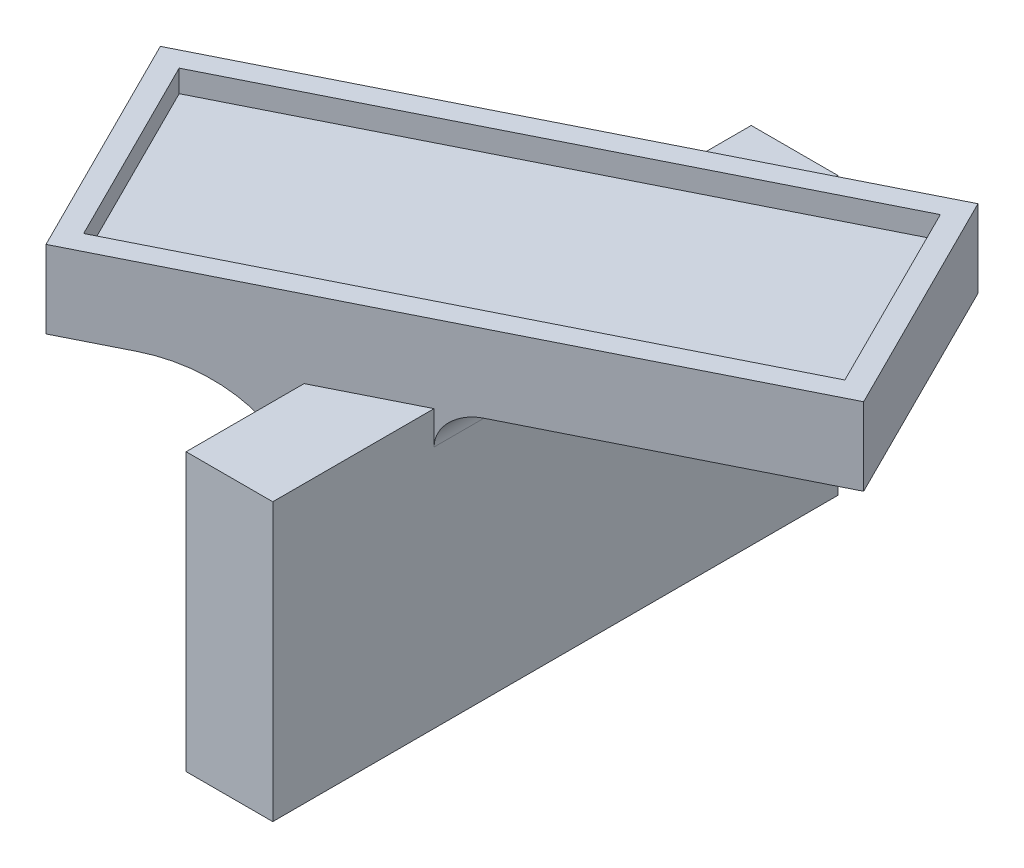
SolidWorks part; units mm, degrees
material "ABS"
ref_plane "Front Plane" through (0, 0, 0) normal (0, 0, 1) x (1, 0, 0)
ref_plane "Top Plane" through (0, 0, 0) normal (0, 1, 0) x (1, 0, 0)
ref_plane "Right Plane" through (0, 0, 0) normal (1, 0, 0) x (0, 0, -1)
sketch "Sketch1" plane through (0, 0, 0) normal (0, 1, 0) x (1, 0, 0)
  line L1 (-3.91, -25.5) -> (3.91, -25.5)
  line L2 (-3.91, -25.5) -> (-3.91, 25.5)
  line L3 (-3.91, 25.5) -> (3.91, 25.5)
  line L4 (3.91, -25.5) -> (3.91, 25.5)
  line L5 (-3.91, -25.5) -> (3.91, 25.5) construction
  line L6 (-3.91, 25.5) -> (3.91, -25.5) construction
  point P0 (0, 0)
extrude "Boss-Extrude1" add sketch "Sketch1" along normal blind 25
sketch "Sketch2" plane through (0, 25, 0) normal (0, 1, 0) x (1, 0, 0)
  line L0 (0, 0) -> (64.6527, 0) construction
  line L1 (4.3382, -8.6764) -> (-21.5791, 43.1582) construction
  line L2 (32.4868, 26.9038) -> (18.5437, 19.9323)
  line L3 (18.5437, 19.9323) -> (27.0721, 2.8756)
  line L4 (27.0721, 2.8756) -> (-18.5437, -19.9323)
  line L5 (-18.5437, -19.9323) -> (-27.0721, -2.8756)
  line L6 (-27.0721, -2.8756) -> (32.4868, 26.9038)
  line L7 (-27.0721, -2.8756) -> (27.0721, 2.8756) construction
  line L8 (18.5437, 19.9323) -> (-18.5437, -19.9323) construction
  line L9 (-19.4381, -22.6156) -> (29.7554, 1.9812)
  line L10 (-3.91, -25.5) -> (3.91, -25.5) construction
  line L11 (29.7554, 1.9812) -> (19.4381, 22.6156)
  line L12 (19.4381, 22.6156) -> (-29.7554, -1.9812)
  line L13 (-29.7554, -1.9812) -> (-19.4381, -22.6156)
  point P5 (0, 0)
  point P12 (0, 0)
  dimension "D1" = 25.5
  dimension "D2" = 51
  dimension "D3" = 25.5
  dimension "D4" = 90
  dimension "D5" = 0
  dimension "D6" = 63.435
  dimension "D7" = 19.07
  dimension "D8" = 2
  dimension "D9" = 2
  dimension "D10" = 2
  dimension "D11" = 2
extrude "Boss-Extrude2" add sketch "Sketch2" along normal blind 5 contours L12 L13 L9 L11
sketch "Sketch3" plane through (0, 30, 0) normal (0, 1, 0) x (1, 0, 0)
  line L0 (-29.7554, -1.9812) -> (-19.4381, -22.6156) construction
  line L1 (19.4381, 22.6156) -> (-29.7554, -1.9812) construction
  line L2 (29.7554, 1.9812) -> (19.4381, 22.6156) construction
  line L4 (29.7554, 1.9812) -> (19.4381, 22.6156)
  line L5 (19.4381, 22.6156) -> (-29.7554, -1.9812)
  line L6 (-29.7554, -1.9812) -> (-19.4381, -22.6156)
  line L7 (-19.4381, -22.6156) -> (29.7554, 1.9812)
  line L11 (-19.4381, -22.6156) -> (29.7554, 1.9812)
  line L18 (-27.2062, -2.8309) -> (18.5884, 20.0665)
  line L19 (18.5884, 20.0665) -> (27.2062, 2.8309)
  line L20 (27.2062, 2.8309) -> (-18.5884, -20.0665) construction
  line L21 (-18.5884, -20.0665) -> (-27.2062, -2.8309)
  line M5 (29.7554, 1.9812) -> (19.4381, 22.6156)
  line M6 (19.4381, 22.6156) -> (-29.7554, -1.9812)
  line M7 (-29.7554, -1.9812) -> (-19.4381, -22.6156)
  line M8 (-19.4381, -22.6156) -> (29.7554, 1.9812)
  dimension "D2" = 1.9
  dimension "D3" = 1.9
  dimension "D4" = 1.9
  dimension "D5" = 1.9
  dimension "D1" = 0
extrude "Boss-Extrude3" add sketch "Sketch3" along normal blind 2 contours L20 L21 L18 L19 M8 M5 M6 M7
fillet "Fillet1" radius 10 1 edges at (-3.91, 25, 1.955)
fillet "Fillet2" radius 3 1 edges at (3.91, 25, -1.955)
sketch "Sketch4" plane through (-3.91, 0, 0) normal (-1, 0, 0) x (0, 0, 1)
  line L1 (-1.5, -5) -> (1.5, -5)
  line L2 (-1.5, -5) -> (-1.5, 5)
  line L3 (-1.5, 5) -> (1.5, 5)
  line L4 (1.5, -5) -> (1.5, 5)
  line L5 (-1.5, -5) -> (1.5, 5) construction
  line L6 (-1.5, 5) -> (1.5, -5) construction
  line L7 (-25.5, 0) -> (25.5, 0) construction
  point P6 (0, 0)
  point P7 (0, 0)
  dimension "D1" = 0
extrude "Boss-Extrude4" add sketch "Sketch4" along normal blind 2.5
chamfer "Chamfer1" distance 1 angle 45 3 edges at (-3.91, 2.5, -1.5) (-3.91, 5, 0) (-3.91, 2.5, 1.5)
